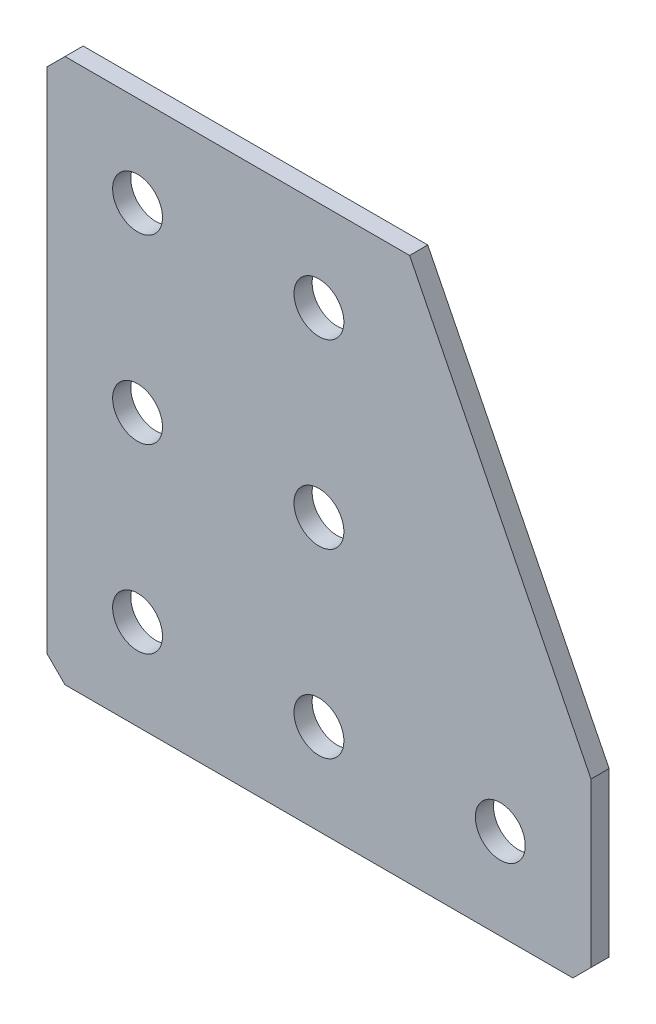
SolidWorks part; units mm, degrees
material "Простая углеродистая сталь"
ref_plane "Спереди(Плоскость XY)" through (0, 0, 0) normal (0, 0, 1) x (1, 0, 0)
ref_plane "Сверху(Плоскость XZ)" through (0, 0, 0) normal (0, 1, 0) x (1, 0, 0)
ref_plane "Справа(Плоскость ZY)" through (0, 0, 0) normal (1, 0, 0) x (0, 0, -1)
sketch "Эскиз1" plane through (0, 0, 0) normal (0, 0, -1) x (1, 0, 0)
  line L0 (0, 0) -> (0, 60)
  line L1 (0, 60) -> (60, 60)
  line L2 (60, 60) -> (60, 40)
  line L3 (60, 40) -> (40, 40) construction
  line L4 (40, 40) -> (40, 0) construction
  line L5 (40, 0) -> (0, 0)
  line L6 (60, 40) -> (40, 0)
  dimension "D1" = 60
  dimension "D2" = 20
  dimension "D3" = 40
extrude "Бобышка-Вытянуть1" add sketch "Эскиз1" along normal blind 2
hole_wizard "Отверстие с зазором M51" positions "Эскиз2" profile "Эскиз3" hole size "M5" standard "DIN" end condition through all
sketch "Эскиз2" plane through (0, 0, -2) normal (0, 0, -1) x (1, 0, 0)
  line L0 (10, 0) -> (10, 60) construction
  line L1 (0, 0) -> (40, 0) construction
  line L2 (60, 60) -> (0, 60) construction
  line L3 (60, 50) -> (0, 50) construction
  line L4 (60, 40) -> (60, 60) construction
  line L5 (0, 60) -> (0, 0) construction
  point P0 (30, 50)
  point P2 (10, 50)
  point P4 (10, 30)
  point P6 (10, 10)
  point P21 (50, 50)
  point P24 (30, 30)
  point P26 (30, 10)
  dimension "D1" = 20
  dimension "D2" = 20
  dimension "D3" = 20
  dimension "D4" = 10
  dimension "D5" = 20
  dimension "D6" = 10
sketch "Эскиз3" plane through (30, -50, -2) normal (1, 0, 0) x (0, 1, 0)
  line L0 (0, 0) -> (0, 2)
  line L1 (0, 2) -> (2.75, 2)
  line L2 (2.75, 2) -> (2.75, 0)
  line L5 (2.75, 0) -> (0, 0)
  line L11 (0, -6.35) -> (0, 107.95) construction
  dimension "Диаметр сквозного отверстия" = 5.5
  dimension "Глубина сквозного отверстия" = 2
chamfer "Фаска1" distance 2 angle 45 3 edges at (0, 0, -1) (60, -60, -1) (0, -60, -1)
